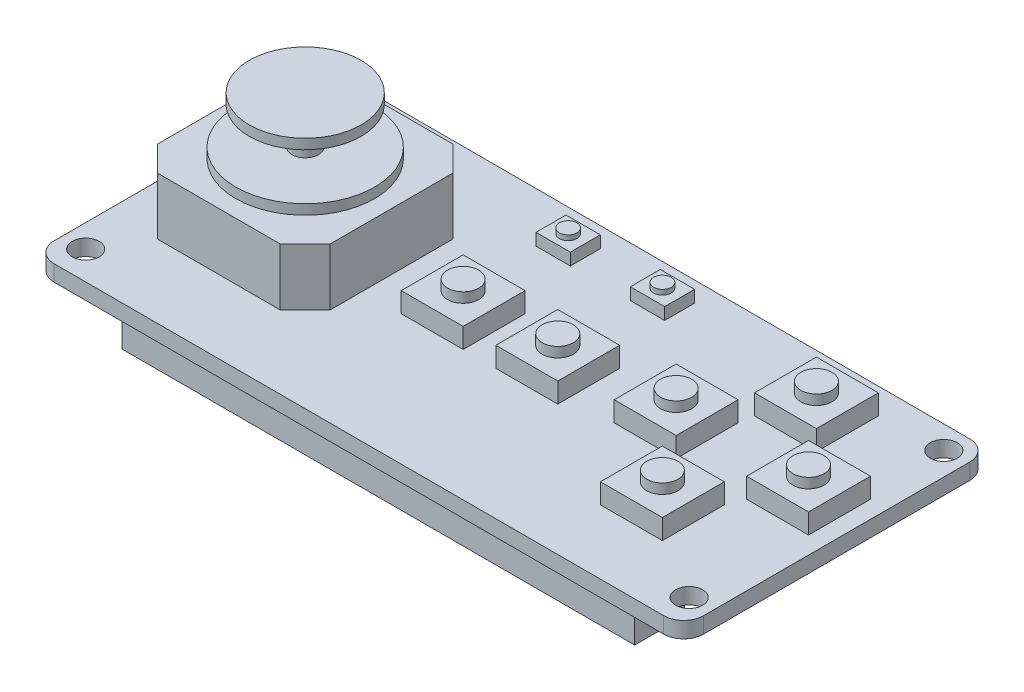
SolidWorks part; units mm, degrees
ref_plane "前视基准面" through (0, 0, 0) normal (0, 0, 1) x (1, 0, 0)
ref_plane "上视基准面" through (0, 0, 0) normal (0, 1, 0) x (1, 0, 0)
ref_plane "右视基准面" through (0, 0, 0) normal (1, 0, 0) x (0, 0, -1)
sketch "草图1" plane through (0, 0, 0) normal (0, 1, 0) x (1, 0, 0)
  line L1 (-35.2962, 18.0875) -> (29.7038, 18.0875)
  line L2 (-35.2962, 18.0875) -> (-35.2962, -12.5525)
  line L3 (-35.2962, -12.5525) -> (29.7038, -12.5525)
  line L4 (29.7038, 18.0875) -> (29.7038, -12.5525)
  dimension "D1" = 65
  dimension "D2" = 30.64
extrude "凸台-拉伸1" add sketch "草图1" along normal blind 1.6
fillet "圆角1" radius 2 4 edges at (-35.2962, 0.8, -18.0875) (-35.2962, 0.8, 12.5525) (29.7038, 0.8, -18.0875) (29.7038, 0.8, 12.5525)
sketch "草图2" plane through (0, 1.6, 0) normal (0, 1, 0) x (1, 0, 0)
  line L0 (-33.2962, -12.5525) -> (27.7038, -12.5525) construction
  line L1 (-35.2962, 16.0875) -> (-35.2962, -10.5525) construction
  line L2 (29.7038, -10.5525) -> (29.7038, 16.0875) construction
  line L3 (27.7038, 18.0875) -> (-33.2962, 18.0875) construction
  circle A0 centre (-32.9962, 15.7875) radius 1.35
  circle A1 centre (27.4038, 15.7875) radius 1.35
  circle A2 centre (27.4038, -9.7025) radius 1.35
  circle A3 centre (-32.9962, -9.7025) radius 1.35
  point P16 (0, 0)
  point P17 (0, 0)
  point P18 (0, 0)
  point P19 (0, 0)
  dimension "D1" = 2.7
  dimension "D2" = 2.85
  dimension "D3" = 2.3
  dimension "D4" = 2.3
  dimension "D5" = 2.3
extrude "切除-拉伸1" cut sketch "草图2" against normal blind 1.6
sketch "草图3" plane through (0, 0, 0) normal (0, -1, 0) x (1, 0, 0)
  line L0 (29.7038, 10.5525) -> (29.7038, -16.0875) construction
  line L1 (23.2038, 5.9525) -> (-28.0962, 5.9525)
  line L2 (23.2038, 5.9525) -> (23.2038, 10.9525)
  line L3 (23.2038, 10.9525) -> (-28.0962, 10.9525)
  line L4 (-28.0962, 5.9525) -> (-28.0962, 10.9525)
  line L5 (-33.2962, 12.5525) -> (27.7038, 12.5525) construction
  dimension "D1" = 51.3
  dimension "D2" = 5
  dimension "D3" = 6.5
  dimension "D4" = 1.6
extrude "凸台-拉伸2" add sketch "草图3" along normal blind 4
sketch "草图4" plane through (0, 1.6, 0) normal (0, 1, 0) x (1, 0, 0)
  line L0 (-35.2962, 16.0875) -> (-35.2962, -10.5525) construction
  line L1 (-32.7862, 12.0575) -> (-15.4862, 12.0575)
  line L2 (-32.7862, 12.0575) -> (-32.7862, -5.2425)
  line L3 (-32.7862, -5.2425) -> (-15.4862, -5.2425)
  line L4 (-15.4862, 12.0575) -> (-15.4862, -5.2425)
  line L5 (27.7038, 18.0875) -> (-33.2962, 18.0875) construction
  dimension "D1" = 17.3
  dimension "D2" = 17.3
  dimension "D3" = 2.51
  dimension "D4" = 6.03
extrude "凸台-拉伸3" add sketch "草图4" along normal blind 5.72
chamfer "倒角1" distance 2.5 angle 45 4 edges at (-15.4862, 4.46, -12.0575) (-32.7862, 4.46, -12.0575) (-32.7862, 4.46, 5.2425) (-15.4862, 4.46, 5.2425)
sketch "草图5" plane through (0, 7.32, 0) normal (0, 1, 0) x (1, 0, 0)
  line L0 (-17.9862, 12.0575) -> (-30.2862, 12.0575) construction
  line L1 (-32.7862, 9.5575) -> (-32.7862, -2.7425) construction
  circle A0 centre (-24.1362, 3.4075) radius 6.95
  point P2 (0, 0)
  point P3 (0, 0)
  point P6 (-24.1362, 12.0575)
  point P7 (0, 0)
  point P10 (-32.7862, 3.4075)
  dimension "D1" = 13.9
extrude "凸台-拉伸4" add sketch "草图5" along normal blind 1
sketch "草图6" plane through (0, 8.32, 0) normal (0, 1, 0) x (1, 0, 0)
  circle A0 centre (-24.1362, 3.4075) radius 1.3261
extrude "凸台-拉伸5" add sketch "草图6" along normal blind 3.72
sketch "草图7" plane through (0, 12.04, 0) normal (0, 1, 0) x (1, 0, 0)
  circle A0 centre (-24.1362, 3.4075) radius 5.6
  dimension "D1" = 11.2
extrude "凸台-拉伸6" add sketch "草图7" along normal blind 1
sketch "草图8" plane through (0, 1.6, 0) normal (0, 1, 0) x (1, 0, 0)
  line L0 (27.7038, 18.0875) -> (-33.2962, 18.0875) construction
  line L1 (-11.6062, 6.6875) -> (-5.4062, 6.6875)
  line L2 (-11.6062, 6.6875) -> (-11.6062, 0.4875)
  line L3 (-11.6062, 0.4875) -> (-5.4062, 0.4875)
  line L4 (-5.4062, 6.6875) -> (-5.4062, 0.4875)
  line L5 (-11.6062, 6.6875) -> (-5.4062, 0.4875) construction
  line L6 (-11.6062, 0.4875) -> (-5.4062, 6.6875) construction
  line L7 (-2.1362, 6.6875) -> (4.0638, 6.6875)
  line L8 (-2.1362, 6.6875) -> (-2.1362, 0.4875)
  line L9 (-2.1362, 0.4875) -> (4.0638, 0.4875)
  line L10 (4.0638, 6.6875) -> (4.0638, 0.4875)
  line L11 (-2.1362, 6.6875) -> (4.0638, 0.4875) construction
  line L12 (-2.1362, 0.4875) -> (4.0638, 6.6875) construction
  line L13 (8.5138, 7.8875) -> (14.7138, 7.8875)
  line L14 (8.5138, 7.8875) -> (8.5138, 1.6875)
  line L15 (8.5138, 1.6875) -> (14.7138, 1.6875)
  line L16 (14.7138, 7.8875) -> (14.7138, 1.6875)
  line L17 (8.5138, 7.8875) -> (14.7138, 1.6875) construction
  line L18 (8.5138, 1.6875) -> (14.7138, 7.8875) construction
  line L19 (14.9338, 15.5075) -> (21.1338, 15.5075)
  line L20 (14.9338, 15.5075) -> (14.9338, 9.3075)
  line L21 (14.9338, 9.3075) -> (21.1338, 9.3075)
  line L22 (21.1338, 15.5075) -> (21.1338, 9.3075)
  line L23 (14.9338, 15.5075) -> (21.1338, 9.3075) construction
  line L24 (14.9338, 9.3075) -> (21.1338, 15.5075) construction
  line L25 (21.7638, 7.8875) -> (27.9638, 7.8875)
  line L26 (21.7638, 7.8875) -> (21.7638, 1.6875)
  line L27 (21.7638, 1.6875) -> (27.9638, 1.6875)
  line L28 (27.9638, 7.8875) -> (27.9638, 1.6875)
  line L29 (21.7638, 7.8875) -> (27.9638, 1.6875) construction
  line L30 (21.7638, 1.6875) -> (27.9638, 7.8875) construction
  line L31 (14.9338, 0.0875) -> (21.1338, 0.0875)
  line L32 (14.9338, 0.0875) -> (14.9338, -6.1125)
  line L33 (14.9338, -6.1125) -> (21.1338, -6.1125)
  line L34 (21.1338, 0.0875) -> (21.1338, -6.1125)
  line L35 (14.9338, 0.0875) -> (21.1338, -6.1125) construction
  line L36 (14.9338, -6.1125) -> (21.1338, 0.0875) construction
  line L37 (-15.4862, -2.7425) -> (-15.4862, 9.5575) construction
  line L38 (29.7038, -10.5525) -> (29.7038, 16.0875) construction
  line L39 (-33.2962, -12.5525) -> (27.7038, -12.5525) construction
  point P0 (-8.5062, 3.5875)
  point P5 (0.9638, 3.5875)
  point P10 (11.6138, 4.7875)
  point P15 (18.0338, 12.4075)
  point P20 (24.8638, 4.7875)
  point P25 (18.0338, -3.0125)
  point P34 (1.0931, 7.4027)
  point P35 (9.236, 6.8896)
  point P36 (15.8412, -2.304)
  point P37 (23.85, 4.976)
  point P38 (17.1092, 12.31)
  point P39 (10.2066, 4.976)
  point P40 (17.1092, -2.7354)
  point P41 (0, 0)
  point P44 (0, 0)
  point P45 (0, 0)
  dimension "D1" = 6.2
  dimension "D2" = 11.4
  dimension "D3" = 3.88
  dimension "D4" = 3.27
  dimension "D5" = 4.45
  dimension "D6" = 10.2
  dimension "D7" = 1.74
  dimension "D8" = 8.57
  dimension "D9" = 6.44
  dimension "D10" = 2.58
extrude "凸台-拉伸7" add sketch "草图8" along normal blind 2
sketch "草图9" plane through (0, 3.6, 0) normal (0, 1, 0) x (1, 0, 0)
  line L0 (-5.4062, 6.6875) -> (-11.6062, 6.6875) construction
  line L1 (-11.6062, 6.6875) -> (-11.6062, 0.4875) construction
  line L2 (4.0638, 6.6875) -> (-2.1362, 6.6875) construction
  line L3 (-2.1362, 6.6875) -> (-2.1362, 0.4875) construction
  line L4 (8.5138, 7.8875) -> (8.5138, 1.6875) construction
  line L5 (14.7138, 7.8875) -> (8.5138, 7.8875) construction
  line L6 (21.1338, 15.5075) -> (14.9338, 15.5075) construction
  line L7 (14.9338, 15.5075) -> (14.9338, 9.3075) construction
  line L8 (27.9638, 7.8875) -> (21.7638, 7.8875) construction
  line L9 (27.9638, 1.6875) -> (27.9638, 7.8875) construction
  line L10 (21.1338, 0.0875) -> (14.9338, 0.0875) construction
  line L11 (21.1338, -6.1125) -> (21.1338, 0.0875) construction
  circle A0 centre (-8.5062, 3.5875) radius 1.56
  circle A1 centre (0.9638, 3.5875) radius 1.56
  circle A2 centre (11.6138, 4.7875) radius 1.56
  circle A3 centre (18.0338, 12.4075) radius 1.56
  circle A4 centre (24.8638, 4.7875) radius 1.56
  circle A5 centre (18.0338, -3.0125) radius 1.56
  point P5 (-8.5062, 6.6875)
  point P9 (-11.6062, 3.5875)
  point P18 (0, 0)
  point P21 (0.9638, 6.6875)
  point P22 (0, 0)
  point P25 (-2.1362, 3.5875)
  point P26 (0, 0)
  point P29 (8.5138, 4.7875)
  point P30 (0, 0)
  point P33 (11.6138, 7.8875)
  point P34 (0, 0)
  point P37 (18.0338, 15.5075)
  point P38 (0, 0)
  point P41 (14.9338, 12.4075)
  point P42 (0, 0)
  point P45 (24.8638, 7.8875)
  point P46 (0, 0)
  point P49 (27.9638, 4.7875)
  point P50 (0, 0)
  point P53 (18.0338, 0.0875)
  point P54 (0, 0)
  point P57 (21.1338, -3.0125)
  dimension "D1" = 3.12
extrude "凸台-拉伸8" add sketch "草图9" along normal blind 1
sketch "草图10" plane through (0, 1.6, 0) normal (0, 1, 0) x (1, 0, 0)
  line L0 (-35.2962, 16.0875) -> (-35.2962, -10.5525) construction
  line L1 (-10.7162, 16.0875) -> (-7.2762, 16.0875)
  line L2 (-10.7162, 16.0875) -> (-10.7162, 13.0875)
  line L3 (-10.7162, 13.0875) -> (-7.2762, 13.0875)
  line L4 (-7.2762, 16.0875) -> (-7.2762, 13.0875)
  line L5 (-10.7162, 16.0875) -> (-7.2762, 13.0875) construction
  line L6 (-10.7162, 13.0875) -> (-7.2762, 16.0875) construction
  line L7 (-1.2762, 16.0875) -> (2.1638, 16.0875)
  line L8 (-1.2762, 16.0875) -> (-1.2762, 13.0875)
  line L9 (-1.2762, 13.0875) -> (2.1638, 13.0875)
  line L10 (2.1638, 16.0875) -> (2.1638, 13.0875)
  line L11 (-1.2762, 16.0875) -> (2.1638, 13.0875) construction
  line L12 (-1.2762, 13.0875) -> (2.1638, 16.0875) construction
  line L13 (27.7038, 18.0875) -> (-33.2962, 18.0875) construction
  point P0 (-8.9962, 14.5875)
  point P5 (0.4438, 14.5875)
  point P14 (0, 0)
  dimension "D1" = 3.44
  dimension "D2" = 3
  dimension "D3" = 3.44
  dimension "D4" = 3
  dimension "D5" = 24.58
  dimension "D6" = 6
  dimension "D7" = 2
extrude "凸台-拉伸9" add sketch "草图10" along normal blind 1.2
sketch "草图11" plane through (0, 2.8, 0) normal (0, 1, 0) x (1, 0, 0)
  line L0 (-7.2762, 16.0875) -> (-10.7162, 16.0875) construction
  line L1 (2.1638, 16.0875) -> (-1.2762, 16.0875) construction
  line L2 (-10.7162, 16.0875) -> (-10.7162, 13.0875) construction
  circle A0 centre (-8.9962, 14.5875) radius 0.875
  circle A1 centre (0.4438, 14.5875) radius 0.875
  point P4 (0, 0)
  point P7 (-8.9962, 16.0875)
  point P8 (0, 0)
  point P11 (0.4438, 16.0875)
  point P12 (0, 0)
  point P15 (-10.7162, 14.5875)
  dimension "D1" = 1.75
extrude "凸台-拉伸10" add sketch "草图11" along normal blind 0.5
